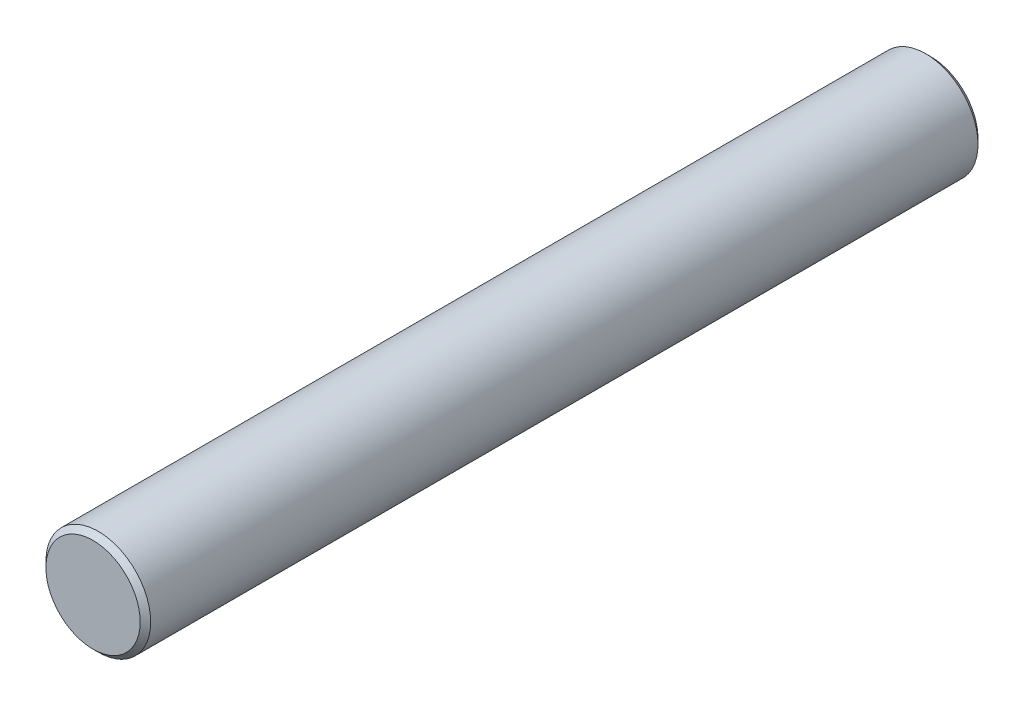
SolidWorks part; units mm, degrees
ref_plane "Plane1" through (0, 0, 0) normal (0, 0, 1) x (1, 0, 0)
ref_plane "Plane2" through (0, 0, 0) normal (0, 1, 0) x (1, 0, 0)
ref_plane "Plane3" through (0, 0, 0) normal (1, 0, 0) x (0, 0, -1)
sketch "Esquisse1" plane through (0, 0, 0) normal (0, 0, 1) x (1, 0, 0)
  circle A0 centre (0, 0) radius 2.5
  dimension "D1" = 5
extrude "Base-Extrusion" add sketch "Esquisse1" along normal blind 40
chamfer "Chanfrein1" distance 0.25 angle 45
